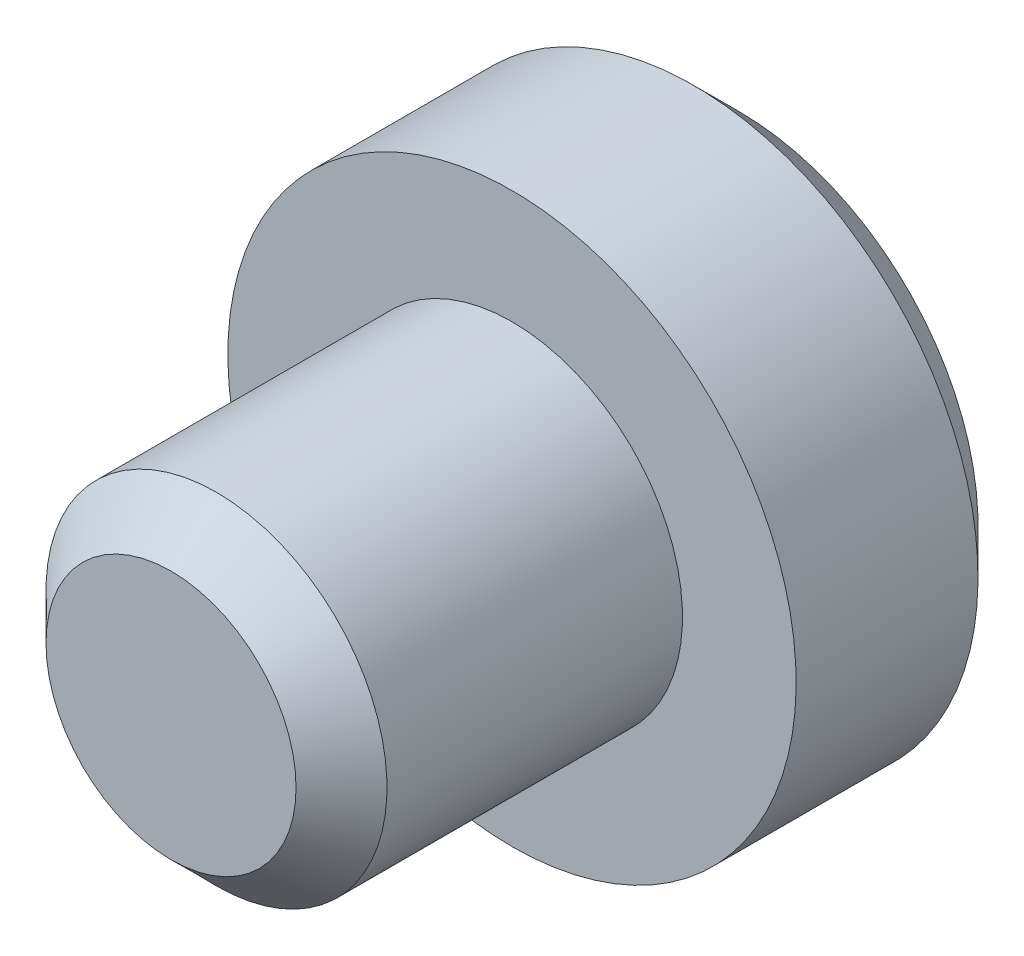
SolidWorks part; units mm, degrees
ref_plane "Front Plane" through (0, 0, 0) normal (0, 0, 1) x (1, 0, 0)
ref_plane "Top Plane" through (0, 0, 0) normal (0, 1, 0) x (1, 0, 0)
ref_plane "Right Plane" through (0, 0, 0) normal (1, 0, 0) x (0, 0, -1)
sketch "Sketch2" plane through (0, 0, 0) normal (1, 0, 0) x (0, 0, -1)
  line L0 (0, 0) -> (-1.4064, 0) construction
  line L1 (0, 0) -> (0, 4893.7954) construction
  line L2 (0, 2.5) -> (-2, 2.5)
  line L3 (-2, 2.5) -> (-2, 1.5)
  line L4 (-2, 1.5) -> (-5, 1.5)
  line L5 (-5, 1.5) -> (-5, 0)
  line L6 (-5, 0) -> (0, 0)
  line L7 (0, 0) -> (0, 2.5)
  dimension "D1" = 2
  dimension "D2" = 1.5
  dimension "D3" = 2.5
  dimension "D4" = 3
revolve "Revolve1" add sketch "Sketch2" angle 360 about L6
sketch "Sketch3" plane through (0, 0, 0) normal (0, 0, -1) x (-1, 0, 0)
  line L1 (1.1684, -0.4981) -> (1.0156, 0.7629)
  line L2 (1.0156, 0.7629) -> (-0.1529, 1.2609)
  line L3 (-0.1529, 1.2609) -> (-1.1684, 0.4981)
  line L4 (-1.1684, 0.4981) -> (-1.0156, -0.7629)
  line L5 (-1.0156, -0.7629) -> (0.1529, -1.2609)
  line L6 (0.1529, -1.2609) -> (1.1684, -0.4981)
  circle A1 centre (0, 0) radius 1.1 construction
  dimension "D1" = 2.2
extrude "Cut-Extrude1" cut sketch "Sketch3" against normal blind 2
chamfer "Chamfer1" distance 0.4 angle 45 2 edges at (0, -1.5, 5) (0, -2.5, 0)
chamfer "Chamfer2" distance 0.1 angle 45 6 edges at (0.4313, -1.0119, 0) (1.092, -0.1324, 0) (0.6607, 0.8795, 0) (-0.4313, 1.0119, 0) (-1.092, 0.1324, 0) (-0.6607, -0.8795, 0)
scale "ｽｹｰﾙ1" scale about centroid uniform scaling yes scale factor 0.894737
